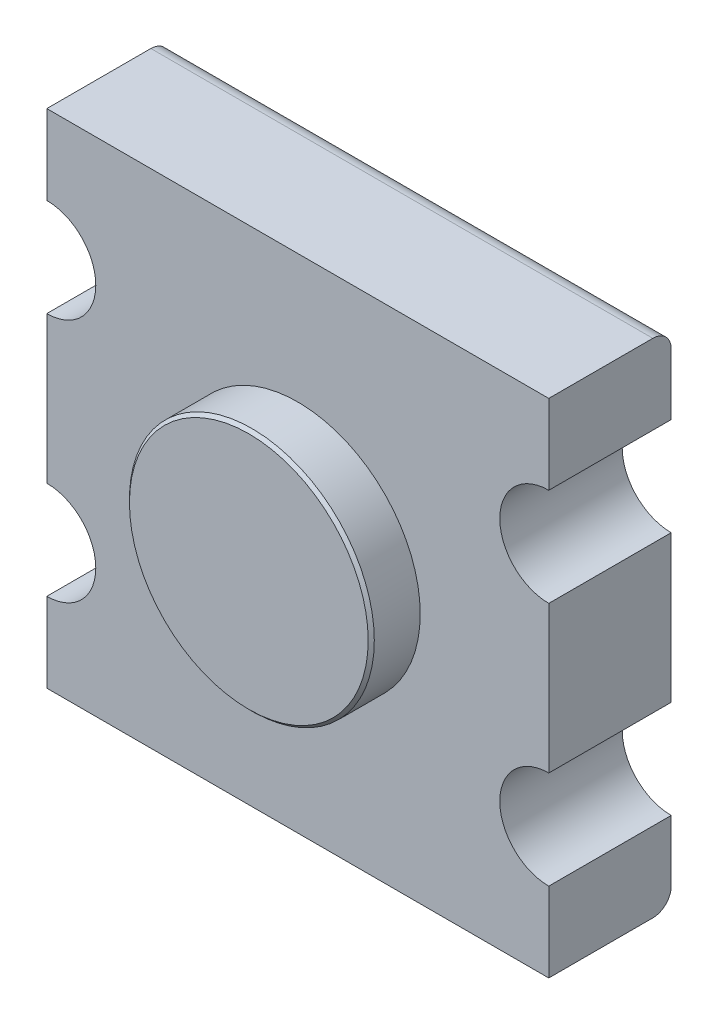
SolidWorks part; units mm, degrees
ref_plane "Front Plane" through (0, 0, 0) normal (0, 0, 1) x (1, 0, 0)
ref_plane "Top Plane" through (0, 0, 0) normal (0, 1, 0) x (1, 0, 0)
ref_plane "Right Plane" through (0, 0, 0) normal (1, 0, 0) x (0, 0, -1)
sketch "Sketch1" plane through (0, 0, 0) normal (0, 0, 1) x (1, 0, 0)
  line L0 (0, 69) -> (0, 82)
  line L1 (0, 0) -> (82, 0)
  line L2 (0, 0) -> (0, 13)
  line L3 (0, 82) -> (82, 82)
  line L4 (82, 0) -> (82, 13)
  line L5 (82, 69) -> (82, 82)
  line L6 (82, 29) -> (82, 53)
  line L7 (0, 29) -> (0, 53)
  arc A0 (0, 53) -> (0, 69) centre (0, 61) ccw
  arc A1 (0, 13) -> (0, 29) centre (0, 21) ccw
  arc A2 (82, 69) -> (82, 53) centre (82, 61) ccw
  arc A3 (82, 29) -> (82, 13) centre (82, 21) ccw
  point P8 (0, 0)
  point P18 (0, 0)
  point P19 (0, 0)
  point P20 (0, 0)
  dimension "D3" = 8
  dimension "D5" = 40
  dimension "D1" = 82
  dimension "D2" = 82
  dimension "D4" = 21
extrude "Boss-Extrude1" add sketch "Sketch1" along normal blind 20
sketch "Sketch2" plane through (0, 0, 20) normal (0, 0, 1) x (1, 0, 0)
  line L0 (82, 29) -> (82, 53) construction
  line L1 (0, 0) -> (82, 0) construction
  circle A0 centre (41, 41) radius 20
  dimension "D1" = 41
  dimension "D2" = 40
  dimension "D3" = 41
extrude "Boss-Extrude2" add sketch "Sketch2" along normal blind 8
chamfer "Chamfer1" distance 0.5 1 edges at (61, 41, 28)
fillet "Fillet1" radius 3 2 edges at (41, 0, 0) (41, 82, 0)
